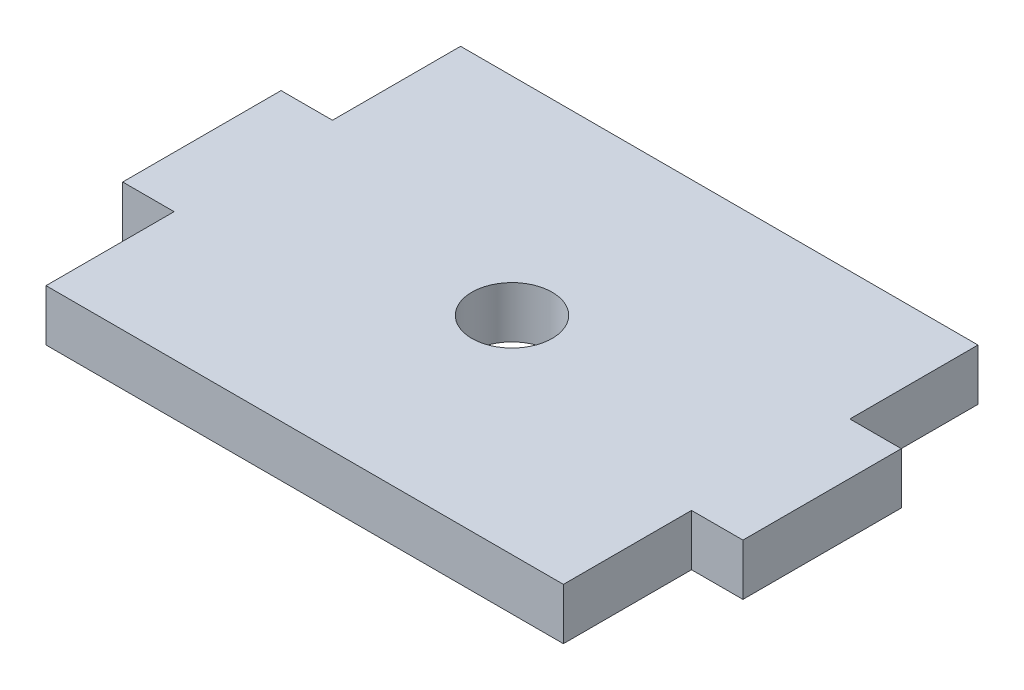
SolidWorks part; units mm, degrees
ref_plane "Front Plane" through (0, 0, 0) normal (0, 0, 1) x (1, 0, 0)
ref_plane "Top Plane" through (0, 0, 0) normal (0, 1, 0) x (1, 0, 0)
ref_plane "Right Plane" through (0, 0, 0) normal (1, 0, 0) x (0, 0, -1)
sketch "Sketch1" plane through (0, 0, 0) normal (0, 1, 0) x (1, 0, 0)
  line L0 (-15.875, -4.7879) -> (-15.875, -12.7) construction
  line L1 (-15.875, 12.7) -> (15.875, 12.7) construction
  line L2 (-15.875, 12.7) -> (-15.875, 4.7879) construction
  line L3 (-15.875, -12.7) -> (15.875, -12.7) construction
  line L4 (15.875, 12.7) -> (15.875, 4.7879) construction
  line L5 (-15.875, 12.7) -> (15.875, -12.7) construction
  line L6 (-15.875, -12.7) -> (15.875, 12.7) construction
  line L7 (15.875, 4.7879) -> (19.05, 4.7879) construction
  line L9 (15.875, -4.7879) -> (19.05, -4.7879) construction
  line L10 (19.05, 4.7879) -> (19.05, -4.7879) construction
  line L11 (-19.05, 0) -> (19.05, 0) construction
  line L12 (-15.9766, 12.8016) -> (15.9766, 12.8016)
  line L13 (-19.05, 4.7879) -> (-15.875, 4.7879) construction
  line L14 (-19.05, 4.7879) -> (-19.05, -4.7879) construction
  line L15 (-19.05, -4.7879) -> (-15.875, -4.7879) construction
  line L17 (15.9766, 12.8016) -> (15.9766, 4.8895)
  line L18 (15.9766, 4.8895) -> (19.1516, 4.8895)
  line L19 (15.875, -4.7879) -> (15.875, -12.7) construction
  line L20 (19.1516, 4.8895) -> (19.1516, -4.8895)
  line L21 (15.9766, -4.8895) -> (19.1516, -4.8895)
  line L22 (15.9766, -4.8895) -> (15.9766, -12.8016)
  line L23 (-15.9766, -12.8016) -> (15.9766, -12.8016)
  line L24 (-15.9766, -4.8895) -> (-15.9766, -12.8016)
  line L25 (-19.1516, -4.8895) -> (-15.9766, -4.8895)
  line L26 (-19.1516, 4.8895) -> (-19.1516, -4.8895)
  line L27 (-19.1516, 4.8895) -> (-15.9766, 4.8895)
  line L28 (-15.9766, 12.8016) -> (-15.9766, 4.8895)
  circle A0 centre (0, 0) radius 2.5797 construction
  circle A1 centre (0, 0) radius 2.4781
  point P0 (0, 0)
  dimension "D6" = 5.1594
  dimension "D1" = 25.4
  dimension "D2" = 3.175
  dimension "D3" = 9.5758
  dimension "D4" = 31.75
  dimension "D5" = 3.175
  dimension "D7" = 0.1016
  dimension "D8" = 0.1016
extrude "Boss-Extrude1" add sketch "Sketch1" along normal mid plane 3.175 contours L19 L9 L10 L7 L4 L1 L2 L13 L14 L15 L0 L3 A0 | L12 L17 L18 L20 L21 L22 L23 L24 L25 L26 L27 L28 | A1
equation "\"D3@Sketch1\"=0.375in+0.002in"
